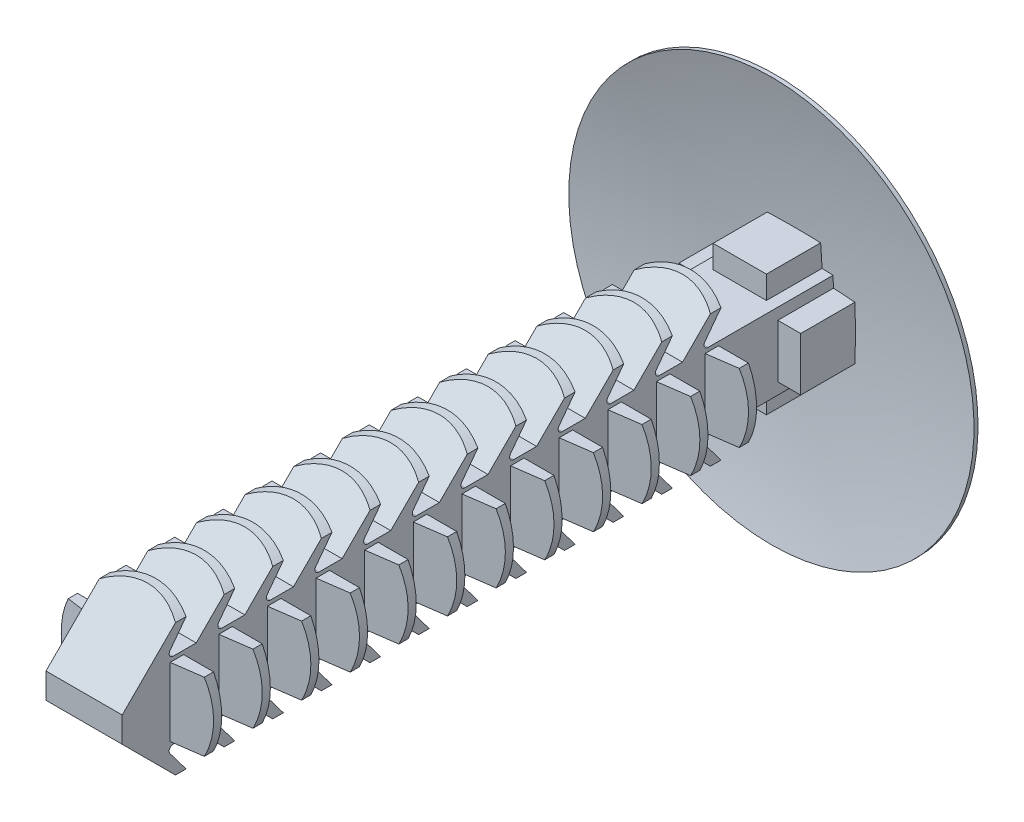
SolidWorks part; units mm, degrees
material "Nylon 101"
ref_plane "Front Plane" through (0, 0, 0) normal (0, 0, 1) x (1, 0, 0)
ref_plane "Top Plane" through (0, 0, 0) normal (0, 1, 0) x (1, 0, 0)
ref_plane "Right Plane" through (0, 0, 0) normal (1, 0, 0) x (0, 0, -1)
sketch "Sketch1" plane through (0, 0, 0) normal (1, 0, 0) x (0, 0, -1)
  line L0 (-11.7602, 0) -> (11.7602, 0) construction
  line L1 (9.779, -6.35) -> (9.779, 6.35) construction
  line L2 (-11.7602, -2.3876) -> (-11.7602, 2.3876) construction
  point P0 (9.779, 0)
  point P4 (0, 0)
  point P9 (9.779, 0)
  point P12 (-11.7602, 0)
sketch "Sketch2" plane through (0, 0, 0) normal (1, 0, 0) x (0, 0, -1)
  line L0 (9.906, -6.35) -> (9.906, 6.35) construction
  line L1 (-11.7602, 0) -> (11.7602, 0) construction
  line L2 (9.779, -6.35) -> (9.779, 6.35) construction
  line L3 (9.906, 6.35) -> (9.779, 6.35)
  line L4 (-11.7602, 0) -> (11.7602, 0) construction
  line L5 (10.5715, 0) -> (11.7602, 0)
  line L6 (10.5715, 0) -> (10.5715, -1.815) construction
  arc A0 (9.906, -6.35) -> (9.906, 6.35) centre (-0.0402, 0) ccw construction
  arc A1 (9.779, 6.35) -> (9.779, -6.35) centre (-0.0402, 0) cw construction
  arc A3 (11.7602, 0) -> (9.906, 6.35) centre (-0.0402, 0) ccw
  arc A4 (10.5715, 0) -> (9.779, 6.35) centre (-15.2655, 0) ccw
  point P3 (9.906, 0)
  dimension "D1" = 0.127
  dimension "D2" = 1.1887
revolve "Revolve1" add sketch "Sketch2" angle 360 about L4
sketch "Sketch3" plane through (0, 0, 0) normal (0, 0, 1) x (1, 0, 0)
  line L1 (-1.1938, -1.1938) -> (1.1938, -1.1938)
  line L2 (-1.1938, -1.1938) -> (-1.1938, 1.1938)
  line L3 (-1.1938, 1.1938) -> (1.1938, 1.1938)
  line L4 (1.1938, -1.1938) -> (1.1938, 1.1938)
  line L5 (-1.1938, -1.1938) -> (1.1938, 1.1938) construction
  line L6 (-1.1938, 1.1938) -> (1.1938, -1.1938) construction
  point P0 (0, 0)
  dimension "D1" = 2.3876
extrude "Boss-Extrude1" add sketch "Sketch3" along normal up to vertex (11.7602 mm away) and the other way up to next separate body up to point (0, 0, 11.7602)
chamfer "Chamfer1" distance 0.7959 angle 45 2 edges at (0, -1.1938, 11.7602) (0, 1.1938, 11.7602)
sketch "Sketch4" plane through (0, 0, 0) normal (1, 0, 0) x (0, 0, -1)
  line L0 (10.5163, 1.1938) -> (-10.9643, 1.1938) construction
  line L1 (-10.9643, 1.1938) -> (-11.7602, 0.3979) construction
  line L2 (10.5163, 1.1938) -> (-10.9643, 1.1938) construction
  line L3 (-10.9643, 1.1938) -> (-11.7602, 0.3979) construction
  line L4 (-11.7602, -2.3876) -> (-11.7602, 2.3876) construction
  line L5 (-11.7602, -2.3876) -> (-11.7602, 2.3876) construction
  line L6 (-10.9643, 1.1938) -> (-9.7705, 2.3876)
  line L7 (-9.7705, 2.3876) -> (-9.5165, 2.3876)
  line L8 (-9.5165, 2.3876) -> (-10.7103, 1.1938) construction
  line L9 (-10.7103, 1.1938) -> (-10.9643, 1.1938) construction
  line L10 (-11.7602, 0) -> (11.7602, 0) construction
  line L11 (-11.7602, 0) -> (11.7602, 0) construction
  line L12 (-10.7103, -1.1938) -> (-10.9643, -1.1938) construction
  line L13 (-9.5165, -2.3876) -> (-10.7103, -1.1938) construction
  line L14 (-9.7705, -2.3876) -> (-9.5165, -2.3876)
  line L15 (-10.9643, -1.1938) -> (-9.7705, -2.3876)
  line L16 (-9.5165, 2.3876) -> (-10.4161, 1.1938)
  line L17 (-10.4161, 1.1938) -> (-10.9643, 1.1938)
  line L18 (-10.9643, -1.1938) -> (-10.4161, -1.1938)
  line L19 (-10.4161, -1.1938) -> (-9.5165, -2.3876)
  dimension "D1" = 0.254
  dimension "D2" = 8
  dimension "D3" = 8
extrude "Boss-Extrude2" add sketch "Sketch4" along normal mid plane 2.3876
sketch "Sketch5" plane through (0, 0, 0) normal (0, 1, 0) x (1, 0, 0)
  line L0 (1.1938, -11.7602) -> (1.1938, 9.779) construction
  line L1 (6.35, 9.779) -> (-6.35, 9.779) construction
  line L2 (0, -11.7602) -> (0, 11.7602) construction
  line L3 (0, -11.7602) -> (0, 11.7602) construction
  line L4 (1.1938, -10.0889) -> (2.3876, -10.0889) construction
  line L5 (2.3876, -10.0889) -> (2.3876, -9.8349)
  line L6 (2.3876, -9.8349) -> (1.1938, -9.8349)
  line L7 (1.1938, -9.8349) -> (1.1938, -10.0889) construction
  line L8 (-1.1938, -9.8349) -> (-1.1938, -10.0889) construction
  line L9 (-2.3876, -9.8349) -> (-1.1938, -9.8349)
  line L10 (-2.3876, -10.0889) -> (-2.3876, -9.8349)
  line L11 (-1.1938, -10.0889) -> (-2.3876, -10.0889) construction
  line L12 (2.3876, -10.0889) -> (1.1938, -10.2567)
  line L13 (1.1938, -10.2567) -> (1.1938, -9.8349)
  line L14 (-2.3876, -10.0889) -> (-1.1938, -10.2567)
  line L15 (-1.1938, -11.7602) -> (-1.1938, -9.7705) construction
  line L16 (-1.1938, -10.2567) -> (-1.1938, -9.8349)
  dimension "D1" = 90
  dimension "D2" = 0.254
  dimension "D3" = 1.1938
  dimension "D4" = 1.6713
  dimension "D5" = 8
  dimension "D6" = 8
extrude "Boss-Extrude3" add sketch "Sketch5" along normal mid plane 2.1488
sketch "Sketch6" plane through (0, 0, 0) normal (0, 0, 1) x (1, 0, 0)
  circle A0 centre (0, 0) radius 2.3876
  dimension "D1" = 4.7752
extrude "Cut-Extrude3" cut sketch "Sketch6" along normal through all flip side to cut contours A0
fillet "Fillet1" radius 0.127 2 edges at (0, -1.1938, 10.4161) (0, 1.1938, 10.4161)
pattern_linear "LPattern2" count 12 spacing 1.524 along (0, 0, -1) of "Boss-Extrude2", "Cut-Extrude3", "Fillet1"
pattern_linear "LPattern3" count 12 spacing 1.524 along (0, 0, -1) of "Boss-Extrude3", "Cut-Extrude3"
combine bodies "Combine1" operation type add bodies to combine 148 104
sketch "Sketch7" plane through (0, 0, 0) normal (0, 0, 1) x (1, 0, 0)
  line L0 (-2.3876, 0) -> (2.3876, 0) construction
  point P4 (0, 0)
  dimension "D1" = 4.7752
ref_plane "Plane1" through (0, 0, -9.779) normal (0, 0, 1) x (1, 0, 0)
sketch "Sketch8" plane through (0, 0, -9.779) normal (0, 0, 1) x (1, 0, 0)
  line L1 (-0.8357, -1.9101) -> (0.8357, -1.9101)
  line L2 (-0.8357, -1.9101) -> (-0.8357, 1.9101)
  line L3 (-0.8357, 1.9101) -> (0.8357, 1.9101)
  line L4 (0.8357, -1.9101) -> (0.8357, 1.9101)
  line L5 (-0.8357, -1.9101) -> (0.8357, 1.9101) construction
  line L6 (-0.8357, 1.9101) -> (0.8357, -1.9101) construction
  point P0 (0, 0)
  dimension "D1" = 3.8202
  dimension "D2" = 1.6713
extrude "Boss-Extrude4" add sketch "Sketch8" along normal blind 0.9906 and the other way up to next (0.9906 mm away)
pattern_circular "CirPattern1" count 2 every 90 about axis through (0, 0, 0) along (0, 0, 1) of "Boss-Extrude4"
sketch "Sketch9" plane through (0, 0, 0) normal (1, 0, 0) x (0, 0, -1)
  line L0 (-11.7602, -1.1938) -> (-11.7602, 1.1938) construction
  line L2 (-11.7602, -2.3876) -> (-11.7602, 2.3876) construction
  point P0 (9.779, -6.35)
  point P5 (-11.7602, 0)
  point P8 (-11.7602, -1.1938)
  point P9 (9.779, 6.35)
  point P11 (11.7602, 0)
  dimension "D1" = 2.3876
equation "\"D1@Sketch3\"=\"For Hole Size@Sketch1\"/2"
equation "\"D1@Chamfer1\"=\"For Hole Size@Sketch1\"/6"
equation "\"D1@Boss-Extrude2\"=\"For Hole Size@Sketch1\"/2"
equation "\"D3@LPattern1\"=\"Length@Sketch1\"/9"
equation "\"D3@Sketch5\"=\"For Hole Size@Sketch1\"/4"
equation "\"D4@Sketch5\"=\"For Hole Size@Sketch1\"*.35"
equation "\"D1@Boss-Extrude3\"=(\"For Hole Size@Sketch1\"/2)*.9"
equation "\"D3@LPattern3\"=\"D3@LPattern2\""
equation "\"D1@Sketch6\"=\"For Hole Size@Sketch1\""
equation "\"D1@LPattern3\"=\"D1@LPattern2\""
equation "\"D1@Sketch7\"=\"For Hole Size@Sketch1\""
equation "\"D1@Boss-Extrude4\"=\"Head Height@Sketch1\"/2"
equation "\"D2@Sketch2\"=\"Head Height@Sketch1\"*.6"
equation "\"D1@Sketch8\"=\"For Hole Size@Sketch1\"*.8"
equation "\"D2@Sketch8\"=\"For Hole Size@Sketch1\"*.35"
equation "\"D1@Sketch9\"=\"For Hole Size@Sketch1\"/2"
